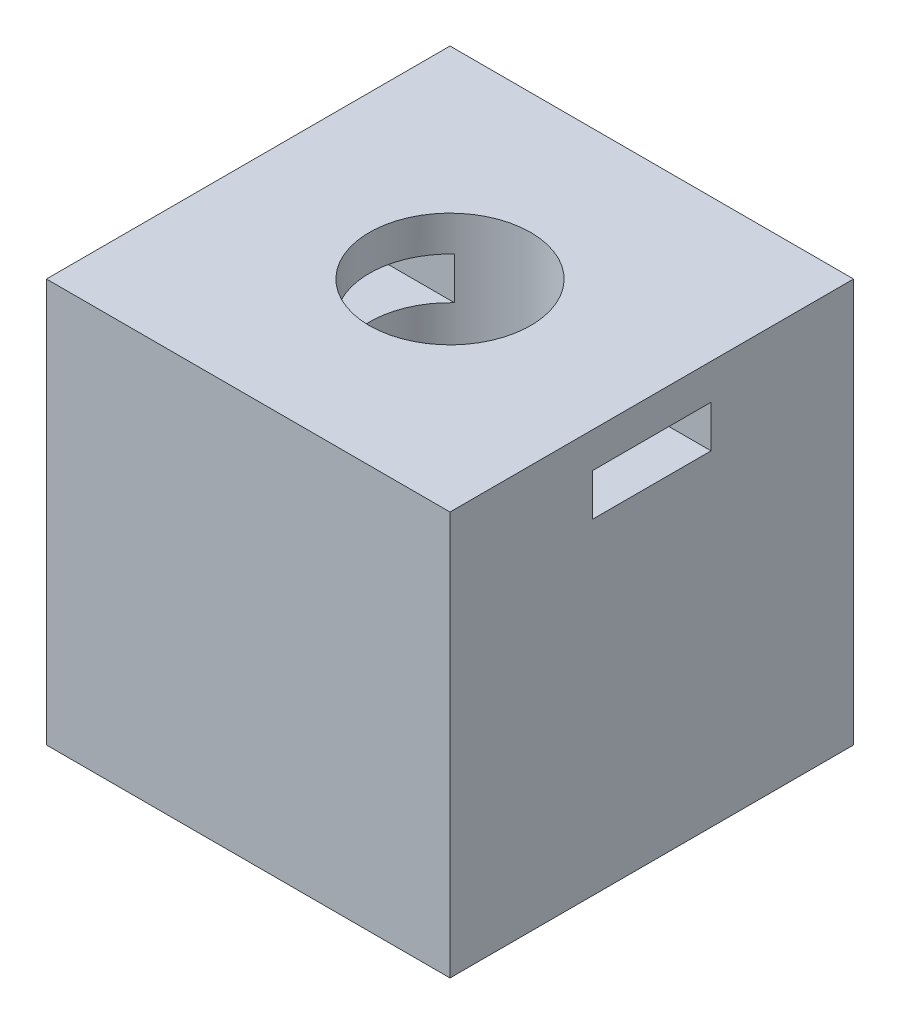
SolidWorks part; units mm, degrees
ref_plane "Plan de face" through (0, 0, 0) normal (0, 0, 1) x (1, 0, 0)
ref_plane "Plan de dessus" through (0, 0, 0) normal (0, 1, 0) x (1, 0, 0)
ref_plane "Plan de droite" through (0, 0, 0) normal (1, 0, 0) x (0, 0, -1)
sketch "Esquisse1" plane through (0, 0, 0) normal (0, 1, 0) x (1, 0, 0)
  line L1 (-7.5, -7.5) -> (7.5, -7.5)
  line L2 (-7.5, -7.5) -> (-7.5, 7.5)
  line L3 (-7.5, 7.5) -> (7.5, 7.5)
  line L4 (7.5, -7.5) -> (7.5, 7.5)
  line L5 (-7.5, -7.5) -> (7.5, 7.5) construction
  line L6 (-7.5, 7.5) -> (7.5, -7.5) construction
  circle A0 centre (0, 0) radius 3
  point P0 (0, 0)
  dimension "D3" = 6
  dimension "D1" = 15
  dimension "D2" = 15
extrude "Boss.-Extru.1" add sketch "Esquisse1" along normal blind 15
sketch "Esquisse2" plane through (7.5, 0, 0) normal (1, 0, 0) x (0, 0, -1)
  line L0 (0, 0) -> (0, 15) construction
  line L1 (-7.5, 0) -> (7.5, 0) construction
  line L2 (-7.5, 15) -> (7.5, 15) construction
  line L4 (7.5, 15) -> (7.5, 0) construction
  line L5 (7.5, 7.5) -> (-7.5, 7.5) construction
  line L6 (-7.5, 15) -> (-7.5, 0) construction
  line L7 (-2.2022, 13.6827) -> (2.2022, 13.6827)
  line L8 (-2.2022, 13.6827) -> (-2.2022, 12.1171)
  line L9 (-2.2022, 12.1171) -> (2.2022, 12.1171)
  line L10 (2.2022, 13.6827) -> (2.2022, 12.1171)
  line L11 (-2.2022, 13.6827) -> (2.2022, 12.1171) construction
  line L12 (-2.2022, 12.1171) -> (2.2022, 13.6827) construction
  point P6 (0, 12.8999)
extrude "Enlèv. mat.-Extru.1" cut sketch "Esquisse2" against normal blind 15
sketch "Esquisse3" plane through (0, 0, 0) normal (0, -1, 0) x (1, 0, 0)
  line L0 (-7.5, 0) -> (7.5, 0) construction
  line L1 (-7.5, -7.5) -> (-7.5, 7.5) construction
  line L2 (7.5, 7.5) -> (7.5, -7.5) construction
  line L3 (0, 7.5) -> (0, -7.5) construction
  line L5 (-7.5, 7.5) -> (7.5, 7.5) construction
  line L6 (7.5, -7.5) -> (-7.5, -7.5) construction
  circle A0 centre (5, 0) radius 1.5
  circle A1 centre (-5, 0) radius 1.5
  dimension "D1" = 3
  dimension "D2" = 5
extrude "Enlèv. mat.-Extru.2" cut sketch "Esquisse3" against normal blind 10
